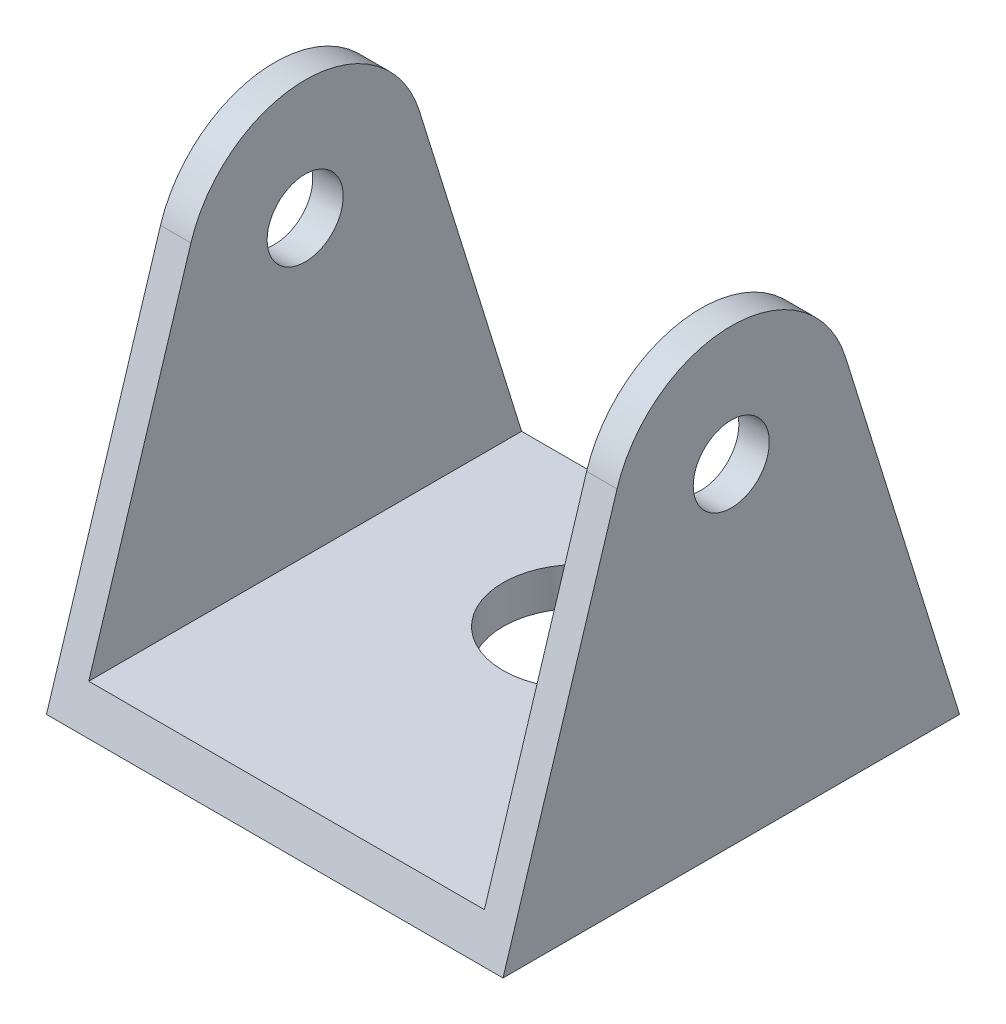
SolidWorks part; units mm, degrees
ref_plane "Front Plane" through (0, 0, 0) normal (0, 0, 1) x (1, 0, 0)
ref_plane "Top Plane" through (0, 0, 0) normal (0, 1, 0) x (1, 0, 0)
ref_plane "Right Plane" through (0, 0, 0) normal (1, 0, 0) x (0, 0, -1)
sketch "Sketch1" plane through (0, 0, 0) normal (0, 1, 0) x (1, 0, 0)
  line L1 (15, -15) -> (-15, -15)
  line L2 (15, -15) -> (15, 15)
  line L3 (15, 15) -> (-15, 15)
  line L4 (-15, -15) -> (-15, 15)
  line L5 (15, -15) -> (-15, 15) construction
  line L6 (15, 15) -> (-15, -15) construction
  point P0 (0, 0)
  dimension "D1" = 30
extrude "Boss-Extrude1" add sketch "Sketch1" along normal blind 2.5
sketch "Sketch2" plane through (0, 2.5, 0) normal (0, 1, 0) x (1, 0, 0)
  line L1 (15, 15) -> (-15, 15) construction
  circle A0 centre (0, 5) radius 5
  dimension "D1" = 10
extrude "Cut-Extrude1" cut sketch "Sketch2" against normal blind 2.5
sketch "Sketch4" plane through (0, 2.5, 0) normal (0, 1, 0) x (1, 0, 0)
  line L0 (-15, -15) -> (15, -15) construction
  line L1 (-15, 15) -> (-13, 15)
  line L2 (-15, 15) -> (-15, -15)
  line L3 (-15, -15) -> (-13, -15)
  line L4 (-13, 15) -> (-13, -15)
  line L6 (15, 15) -> (13, 15)
  line L7 (15, 15) -> (15, -15)
  line L8 (15, -15) -> (13, -15)
  line L9 (13, 15) -> (13, -15)
  dimension "D1" = 2
  dimension "D2" = 2
extrude "Boss-Extrude2" add sketch "Sketch4" along normal blind 31.75
sketch "Sketch5" plane through (-15, 0, 0) normal (-1, 0, 0) x (0, 0, 1)
  line L1 (-15, 0) -> (15, 0) construction
  circle A0 centre (0, 21.75) radius 2.5
  dimension "D1" = 21.75
  dimension "D2" = 5
extrude "Cut-Extrude2" cut sketch "Sketch5" against normal blind 30.75
sketch "Sketch6" plane through (-15, 0, 0) normal (-1, 0, 0) x (0, 0, 1)
  line L0 (-15, 0) -> (-7.5059, 24.0854)
  line L1 (15, 0) -> (7.5059, 24.0854)
  line L2 (-15, 0) -> (-15, 34.25)
  line L3 (-15, 34.25) -> (15, 34.25)
  line L4 (15, 34.25) -> (15, 0)
  arc A0 (7.5059, 24.0854) -> (-7.5059, 24.0854) centre (0, 21.75) ccw
extrude "Cut-Extrude3" cut sketch "Sketch6" against normal blind 30.75
